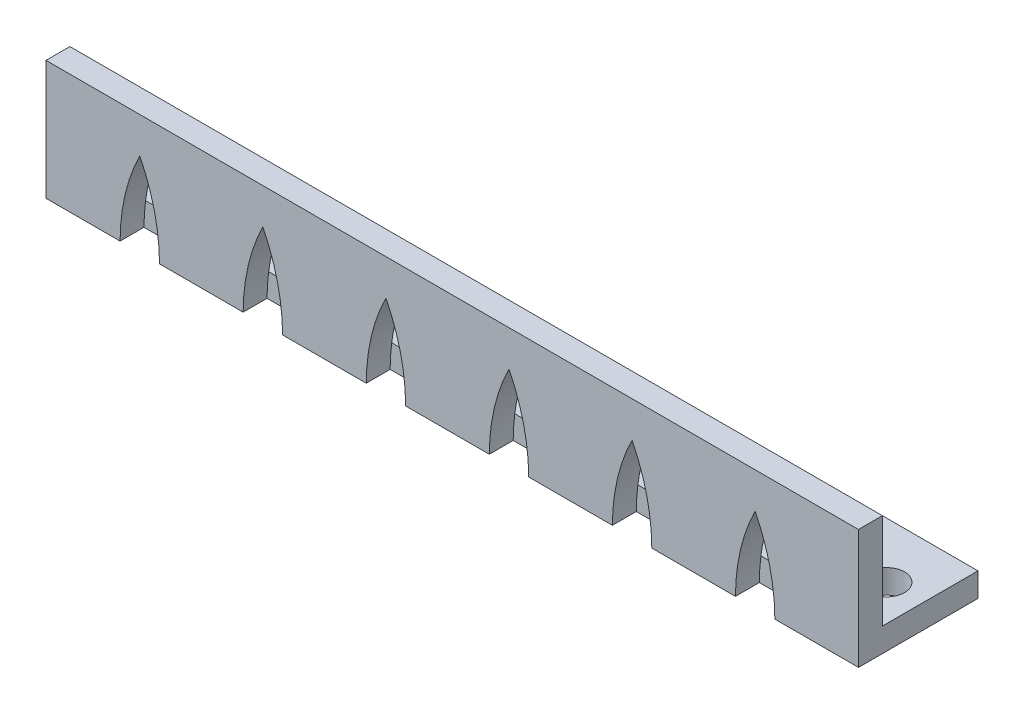
SolidWorks part; units mm, degrees
material "ABS"
ref_plane "Front Plane" through (0, 0, 0) normal (0, 0, 1) x (1, 0, 0)
ref_plane "Top Plane" through (0, 0, 0) normal (0, 1, 0) x (1, 0, 0)
ref_plane "Right Plane" through (0, 0, 0) normal (1, 0, 0) x (0, 0, -1)
ref_plane "Front Plane1" through (0, 0, 5) normal (0, 0, 1) x (1, 0, 0)
sketch "Sketch1" plane through (0, 0, 0) normal (0, 1, 0) x (1, 0, 0)
  line L0 (-34, 5) -> (34, -5) construction
  line L1 (-34, 5) -> (34, 5)
  line L2 (-34, 5) -> (-34, -5)
  line L3 (-34, -5) -> (34, -5)
  line L4 (34, 5) -> (34, -5)
  circle A0 centre (-29, 0.35) radius 1.5025
  circle A1 centre (-19, 0.35) radius 1.5025
  circle A2 centre (-9, 0.35) radius 1.5025
  circle A3 centre (1, 0.35) radius 1.5025
  circle A4 centre (11, 0.35) radius 1.5025
  circle A5 centre (21, 0.35) radius 1.5025
  circle A6 centre (31, 0.35) radius 1.5025
  dimension "D3" = 3.005
  dimension "D4" = 5
  dimension "D5" = 5.35
  dimension "D8" = 5.35
  dimension "D1" = 68
  dimension "D2" = 10
  dimension "D7" = 3
  dimension "D6" = 7
extrude "Boss-Extrude1" add sketch "Sketch1" along normal blind 10
sketch "Sketch2" plane through (0, 0, 0) normal (0, 0, 1) x (1, 0, 0)
  line L0 (34, 10) -> (34, 0) construction
  line L1 (-34, 10) -> (34, 10)
  line L2 (-34, 10) -> (-34, 2)
  line L3 (-34, 2) -> (34, 2)
  line L4 (34, 10) -> (34, 2)
  dimension "D1" = 8
extrude "Cut-Extrude1" cut sketch "Sketch2" against normal up to next and the other way blind 3
sketch "Sketch3" plane through (0, 0, 5) normal (0, 0, 1) x (1, 0, 0)
  line L0 (26.18, 5) -> (24.52, 5) construction
  line L1 (24.52, 10) -> (24.52, 0) construction
  line L2 (34, 10) -> (34, 0) construction
  line L3 (23.7, 0) -> (27, 0)
  line L4 (-34, 10) -> (34, 10) construction
  line L5 (-34, 0) -> (34, 0) construction
  line L6 (23.7, 10) -> (23.7, 0) construction
  line L7 (25.35, 10) -> (25.35, 0) construction
  line L8 (27, 10) -> (27, 0) construction
  line L9 (26.18, 10) -> (26.18, 0) construction
  line L10 (13.4, 0) -> (16.7, 0)
  line L11 (3.1, 0) -> (6.4, 0)
  line L12 (-7.2, 0) -> (-3.9, 0)
  line L13 (-17.5, 0) -> (-14.2, 0)
  line L14 (-27.8, 0) -> (-24.5, 0)
  spline S0 degree 2 poles (25.35, 7) (23.7242, 3.7285) (23.7, 0) knots 0 0 0 1 1 1
  spline S1 degree 2 poles (25.35, 7) (26.9758, 3.7285) (27, 0) knots 0 0 0 1 1 1
  spline S2 degree 2 poles (15.05, 7) (16.6758, 3.7285) (16.7, 0) knots 0 0 0 1 1 1
  spline S3 degree 2 poles (15.05, 7) (13.4242, 3.7285) (13.4, 0) knots 0 0 0 1 1 1
  spline S4 degree 2 poles (4.75, 7) (6.3758, 3.7285) (6.4, 0) knots 0 0 0 1 1 1
  spline S5 degree 2 poles (4.75, 7) (3.1242, 3.7285) (3.1, 0) knots 0 0 0 1 1 1
  spline S6 degree 2 poles (-5.55, 7) (-3.9242, 3.7285) (-3.9, 0) knots 0 0 0 1 1 1
  spline S7 degree 2 poles (-5.55, 7) (-7.1758, 3.7285) (-7.2, 0) knots 0 0 0 1 1 1
  spline S8 degree 2 poles (-15.85, 7) (-14.2242, 3.7285) (-14.2, 0) knots 0 0 0 1 1 1
  spline S9 degree 2 poles (-15.85, 7) (-17.4758, 3.7285) (-17.5, 0) knots 0 0 0 1 1 1
  spline S10 degree 2 poles (-26.15, 7) (-24.5242, 3.7285) (-24.5, 0) knots 0 0 0 1 1 1
  spline S11 degree 2 poles (-26.15, 7) (-27.7758, 3.7285) (-27.8, 0) knots 0 0 0 1 1 1
  point P14 (25.35, 7)
  point P15 (24.52, 5)
  point P16 (26.18, 5)
  dimension "D1" = 1.65
  dimension "D2" = 1.65
  dimension "D3" = 0.83
  dimension "D4" = 0.83
  dimension "D5" = 7
  dimension "D6" = 5
  dimension "D7" = 7
  dimension "D8" = 6
extrude "Cut-Extrude2" cut sketch "Sketch3" against normal blind 2
